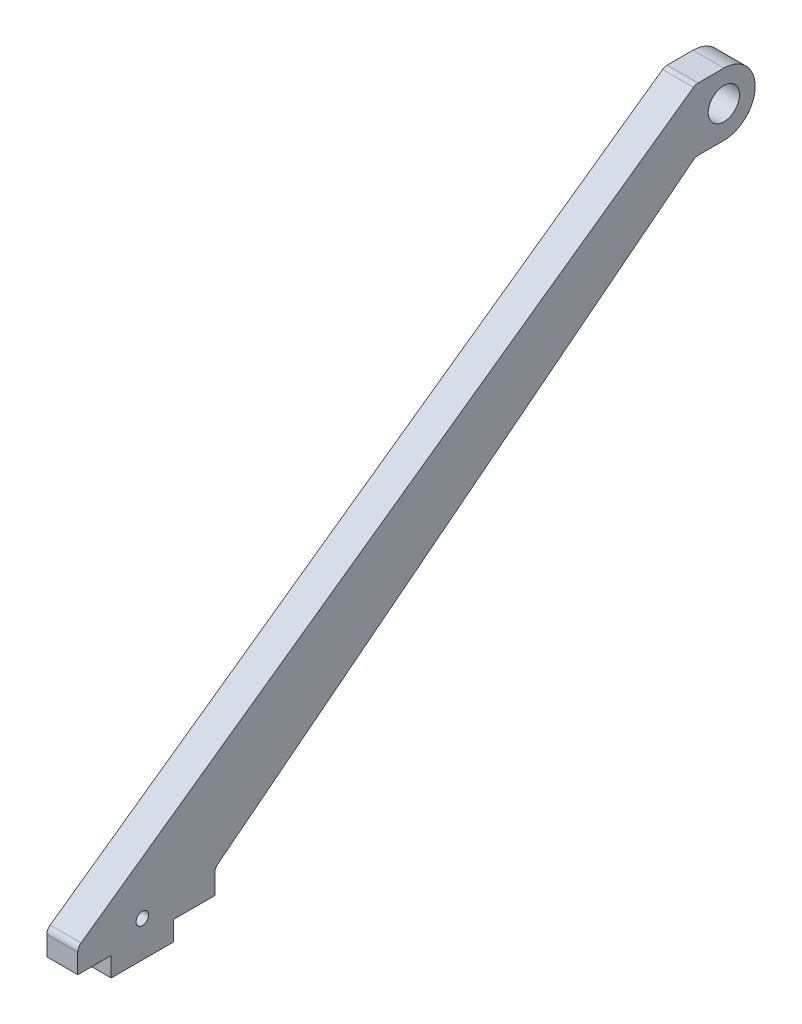
SolidWorks part; units mm, degrees
ref_plane "Plan de face" through (0, 0, 0) normal (0, 0, 1) x (1, 0, 0)
ref_plane "Plan de dessus" through (0, 0, 0) normal (0, 1, 0) x (1, 0, 0)
ref_plane "Plan de droite" through (0, 0, 0) normal (1, 0, 0) x (0, 0, -1)
sketch "Esquisse1" plane through (0, 0, 0) normal (1, 0, 0) x (0, 0, -1)
  line L0 (37.9609, 1.9844) -> (37.9609, 6.9844)
  line L1 (37.9609, 6.9844) -> (29.4109, 6.9844)
  line L2 (37.9609, 1.9844) -> (53.8609, 1.9844)
  line L3 (53.8609, 1.9844) -> (53.8609, 6.9844)
  line L4 (53.8609, 6.9844) -> (64.4109, 6.9844)
  line L5 (187.1755, 124.9844) -> (29.4109, 12.9844)
  line L6 (64.4109, 6.9844) -> (64.4109, 12.9844)
  line L7 (194.4109, 124.9844) -> (187.1755, 124.9844)
  line L8 (194.4109, 108.9844) -> (187.1755, 108.9844)
  line L9 (64.4109, 12.9844) -> (187.1755, 108.9844)
  line L10 (29.4109, 12.9844) -> (29.4109, 6.9844)
  arc A1 (194.4109, 124.9844) -> (194.4109, 108.9844) centre (194.4109, 116.9844) cw
  dimension "D5" = 10.55
  dimension "D8" = 130
  dimension "D1" = 15.9
  dimension "D2" = 5
  dimension "D3" = 5
  dimension "D6" = 6
  dimension "D7" = 8.55
  dimension "D9" = 110
  dimension "D11" = 16
extrude "Boss.-Extru.1" add sketch "Esquisse1" along normal blind 7.9 contours L1 L10 L5 L7 A1 L8 L9 L6 L4 L3 L2 L0
sketch "Esquisse2" plane through (7.9, 0, 0) normal (1, 0, 0) x (0, 0, -1)
  line L0 (37.9609, 1.9844) -> (53.8609, 1.9844) construction
  line L2 (64.4109, 6.9844) -> (64.4109, 12.9844) construction
  circle A0 centre (45.9109, 11.1844) radius 1.6
  circle A1 centre (194.4109, 117.1189) radius 4
  dimension "D1" = 9.2
  dimension "D2" = 3.2
  dimension "D4" = 8
  dimension "D3" = 18.5
extrude "Enlèv. mat.-Extru.1" cut sketch "Esquisse2" against normal through all
fillet "Congé1" radius 2 4 edges at (3.95, 12.9844, -29.4109) (3.95, 12.9844, -64.4109) (3.95, 108.9844, -187.1755) (3.95, 124.9844, -187.1755)
